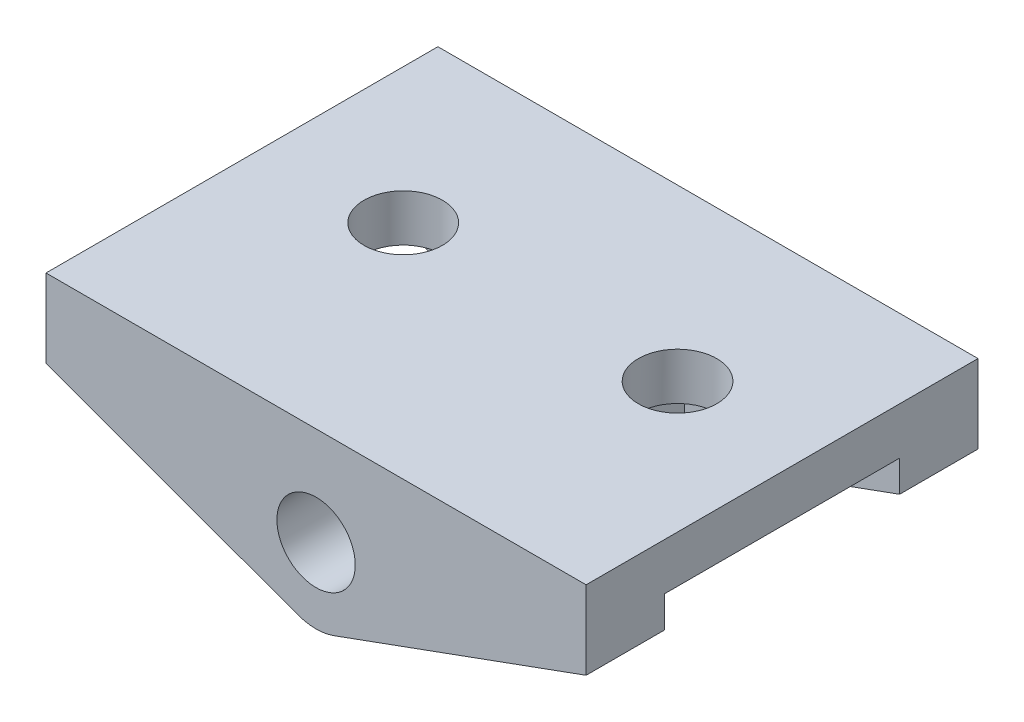
SolidWorks part; units mm, degrees
ref_plane "Alzado" through (0, 0, 0) normal (0, 0, 1) x (1, 0, 0)
ref_plane "Planta" through (0, 0, 0) normal (0, 1, 0) x (1, 0, 0)
ref_plane "Vista lateral" through (0, 0, 0) normal (1, 0, 0) x (0, 0, -1)
sketch "Croquis2" plane through (0, 0, 0) normal (0, 0, 1) x (1, 0, 0)
  line L0 (0, 0) -> (0, -3) construction
  line L1 (-0.684, -2.751) -> (-10.3366, 0.7622)
  line L2 (0.684, -2.751) -> (10.3366, 0.7622)
  line L3 (-10.3366, 0.7622) -> (-10.3366, 3.7622)
  line L4 (-10.3366, 3.7622) -> (10.3366, 3.7622)
  line L5 (10.3366, 3.7622) -> (10.3366, 0.7622)
  circle A0 centre (0, 0) radius 1.5
  arc A1 (0.684, -2.751) -> (-0.684, -2.751) centre (0, -0.8716) cw
  dimension "D1" = 3
  dimension "D7" = 2
  dimension "D2" = 3
  dimension "D3" = 70
  dimension "D4" = 70
  dimension "D5" = 11
  dimension "D6" = 11
  dimension "D8" = 3
extrude "Saliente-Extruir2" add sketch "Croquis2" along normal blind 15
sketch "Croquis3" plane through (0, 3.7622, 0) normal (0, 1, 0) x (1, 0, 0)
  line L0 (10.3366, -15) -> (10.3366, 0) construction
  line L1 (10.3366, 0) -> (-10.3366, 0) construction
  circle A0 centre (5.3366, -6.5) radius 1.5
  circle A1 centre (-5.1634, -6.5) radius 1.5
  dimension "D3" = 3
  dimension "D4" = 3
  dimension "D1" = 10.5
  dimension "D2" = 5
  dimension "D5" = 6.5
extrude "Cortar-Extruir1" cut sketch "Croquis3" against normal through all
ref_plane "Plano1" through (0, 0, 12) normal (0, 0, 1) x (1, 0, 0)
sketch "Croquis4" plane through (0, 0, 12) normal (0, 0, 1) x (1, 0, 0)
  line L1 (0.684, -2.751) -> (10.3366, 0.7622) construction
  line L2 (10.3366, 0.7622) -> (10.3366, 1.9622)
  line L3 (2.1034, -2.2344) -> (10.3366, 0.7622)
  line L4 (10.3366, 0.7622) -> (10.3366, 3.7622) construction
  line L5 (10.3366, 1.9622) -> (2.1034, 1.9622)
  line L6 (2.1034, 1.9622) -> (2.1034, -2.2344)
  dimension "D1" = 1.2
  dimension "D2" = 4.1966
extrude "Cortar-Extruir2" cut sketch "Croquis4" against normal blind 9
sketch "Croquis5" plane through (0, 0, 12) normal (0, 0, 1) x (1, 0, 0)
  line L0 (-10.3366, 0.7622) -> (-0.684, -2.751) construction
  line L1 (-10.3366, 0.7622) -> (-2.0942, -2.2378)
  line L2 (-10.3366, 0.7622) -> (-10.3366, 1.9622)
  line L3 (-10.3366, 3.7622) -> (-10.3366, 0.7622) construction
  line L4 (-10.3366, 1.9622) -> (-2.0942, 1.9622)
  line L5 (-2.0942, 1.9622) -> (-2.0942, -2.2378)
  dimension "D1" = 1.2
  dimension "D2" = 4.2
extrude "Cortar-Extruir3" cut sketch "Croquis5" against normal blind 9
